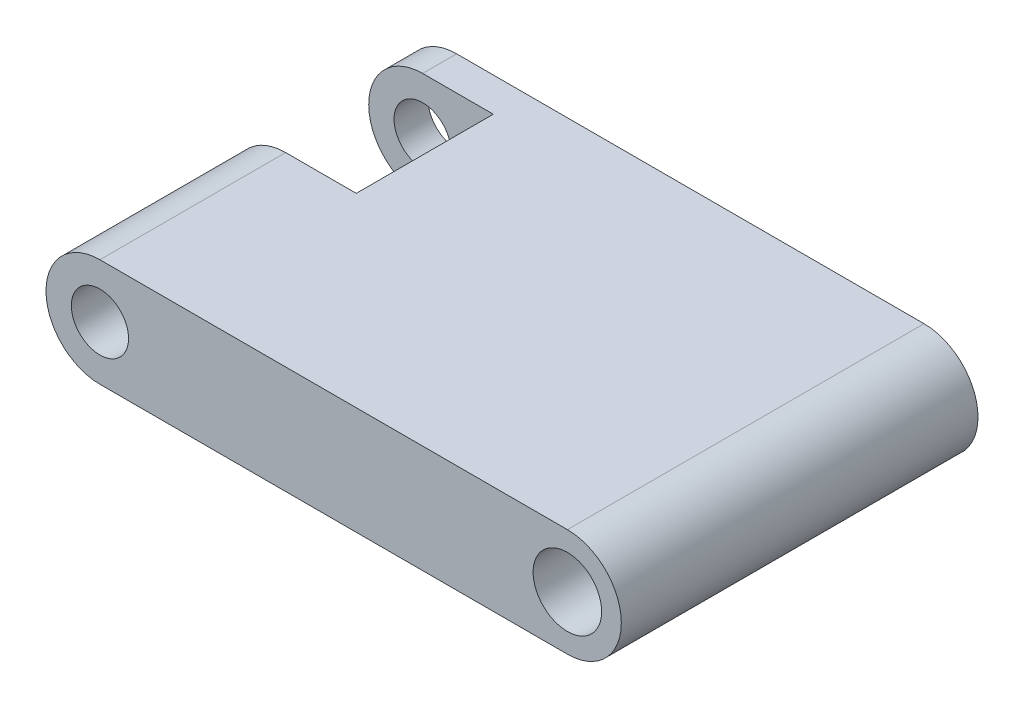
SolidWorks part; units mm, degrees
ref_plane "Front Plane" through (0, 0, 0) normal (0, 0, 1) x (1, 0, 0)
ref_plane "Top Plane" through (0, 0, 0) normal (0, 1, 0) x (1, 0, 0)
ref_plane "Right Plane" through (0, 0, 0) normal (1, 0, 0) x (0, 0, -1)
sketch "Sketch5" plane through (0, 0, 0) normal (0, 0, 1) x (1, 0, 0)
  line L0 (-20.6375, 0) -> (20.6375, 0) construction
  line L1 (-20.6375, 4.7625) -> (20.6375, 4.7625)
  line L2 (-20.6375, -4.7625) -> (20.6375, -4.7625)
  line L3 (20.6375, 0) -> (25.4, 0) construction
  line L4 (-20.6375, 0) -> (-25.4, 0) construction
  arc A0 (-20.6375, 4.7625) -> (-20.6375, -4.7625) centre (-20.6375, 0) ccw
  arc A1 (20.6375, -4.7625) -> (20.6375, 4.7625) centre (20.6375, 0) ccw
  circle A2 centre (-20.6375, 0) radius 2.525
  circle A3 centre (20.6375, 0) radius 3.025
  point P3 (0, 0)
  dimension "D3" = 5.05
  dimension "D4" = 6.05
  dimension "D1" = 9.525
  dimension "D2" = 50.8
extrude "Boss-Extrude2" add sketch "Sketch5" along normal mid plane 31.496
sketch "Sketch6" plane through (0, 0, 0) normal (0, 1, 0) x (1, 0, 0)
  line L0 (0, 0) -> (-28.2574, 0) construction
  line L1 (-25.4, 15.748) -> (-12.7, 15.748) construction
  line L2 (-25.4, 15.748) -> (-25.4, 12.748) construction
  line L3 (-25.4, 12.748) -> (-12.7, 12.748) construction
  line L4 (-12.7, 15.748) -> (-12.7, 12.748) construction
  line L5 (-25.4, 15.748) -> (-25.4, -15.748) construction
  line L6 (-12.7, -15.748) -> (-12.7, -12.748) construction
  line L7 (-25.4, -12.748) -> (-12.7, -12.748) construction
  line L8 (-25.4, -15.748) -> (-25.4, -12.748) construction
  line L9 (-25.4, -15.748) -> (-12.7, -15.748) construction
  line L11 (-14.4, 0.648) -> (-25.4, 0.648)
  line L12 (-14.4, 0.648) -> (-14.4, 12.748)
  line L13 (-14.4, 12.748) -> (-25.4, 12.748)
  line L14 (-25.4, 0.648) -> (-25.4, 12.748)
  line L15 (-14.4, 0.648) -> (-25.4, 12.748) construction
  line L16 (-14.4, 12.748) -> (-25.4, 0.648) construction
  point P14 (-19.9, 6.698)
  point P19 (0, 0)
  point P20 (0, 0)
  dimension "D1" = 3
  dimension "D2" = 12.7
  dimension "D3" = 12.1
  dimension "D4" = 11
extrude "Cut-Extrude2" cut sketch "Sketch6" against normal mid plane 25.4
